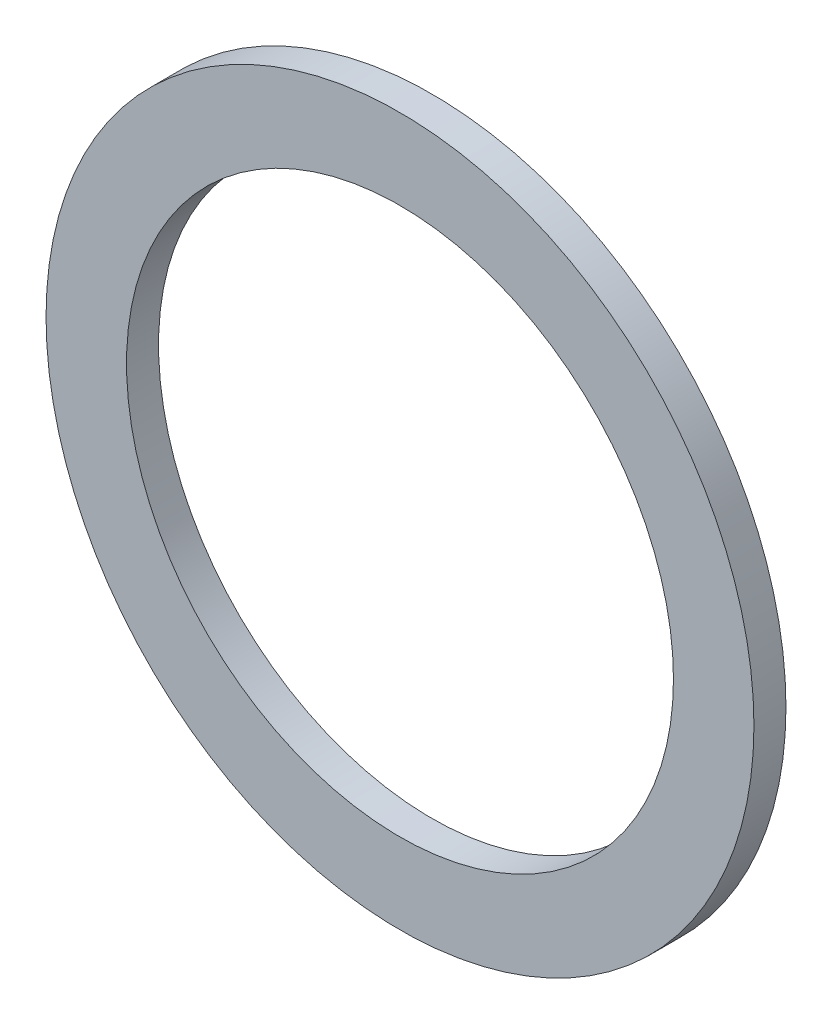
SolidWorks part; units mm, degrees
ref_plane "Front Plane" through (0, 0, 0) normal (0, 0, 1) x (1, 0, 0)
ref_plane "Top Plane" through (0, 0, 0) normal (0, 1, 0) x (1, 0, 0)
ref_plane "Right Plane" through (0, 0, 0) normal (1, 0, 0) x (0, 0, -1)
sketch "Sketch3" plane through (0, 0, 0) normal (0, 0, 1) x (1, 0, 0)
  circle A0 centre (0, 0) radius 19.35
  circle A1 centre (0, 0) radius 14.95
  dimension "D1" = 38.7
  dimension "D2" = 29.9
extrude "Boss-Extrude1" add sketch "Sketch3" along normal blind 1.75
